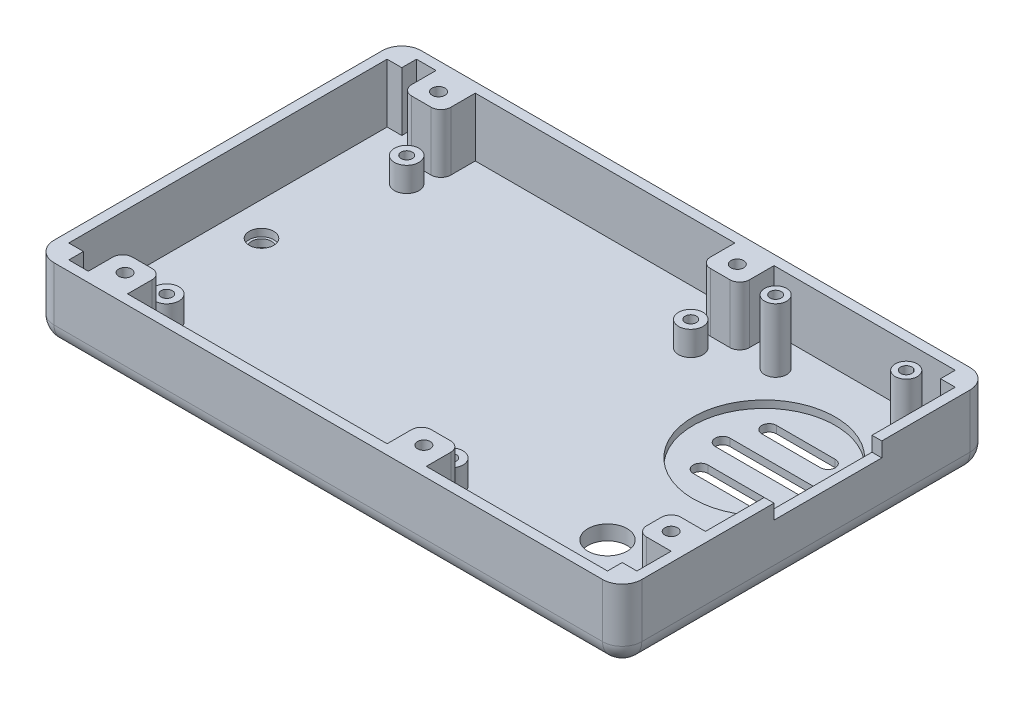
SolidWorks part; units mm, degrees
ref_plane "Front Plane" through (0, 0, 0) normal (0, 0, 1) x (1, 0, 0)
ref_plane "Top Plane" through (0, 0, 0) normal (0, 1, 0) x (1, 0, 0)
ref_plane "Right Plane" through (0, 0, 0) normal (1, 0, 0) x (0, 0, -1)
sketch "Sketch1" plane through (0, 0, 0) normal (0, 1, 0) x (1, 0, 0)
  line L1 (-60, 37.5) -> (60, 37.5)
  line L2 (-60, 37.5) -> (-60, -37.5)
  line L3 (-60, -37.5) -> (60, -37.5)
  line L4 (60, 37.5) -> (60, -37.5)
  line L5 (-60, 37.5) -> (60, -37.5) construction
  line L6 (-60, -37.5) -> (60, 37.5) construction
  point P0 (0, 0)
  dimension "D1" = 120
  dimension "D2" = 75
extrude "Main Structure" add sketch "Sketch1" along normal blind 15
sketch "Sketch2" plane through (0, 15, 0) normal (0, 1, 0) x (1, 0, 0)
  line L1 (-58, -35.5) -> (58, -35.5)
  line L2 (-58, -35.5) -> (-58, 35.5)
  line L3 (-58, 35.5) -> (58, 35.5)
  line L4 (58, -35.5) -> (58, 35.5)
  line L5 (-58, -35.5) -> (58, 35.5) construction
  line L6 (-58, 35.5) -> (58, -35.5) construction
  point P0 (0, 0)
  dimension "D1" = 71
  dimension "D2" = 116
extrude "Inside Cut" cut sketch "Sketch2" against normal blind 12
sketch "Sketch3" plane through (0, 3, 0) normal (0, 1, 0) x (1, 0, 0)
  line L0 (-58, 35.5) -> (-58, -35.5) construction
  line L1 (-58, -35.5) -> (58, -35.5) construction
  line L2 (58, 35.5) -> (-58, 35.5) construction
  circle A0 centre (-46, -24.5) radius 2.5
  circle A1 centre (-46, 24.5) radius 2.5
  circle A2 centre (-46, 24.5) radius 1.15
  circle A3 centre (-46, -24.5) radius 1.15
  circle A4 centre (12, 24.5) radius 2.5
  circle A5 centre (12, -24.5) radius 2.5
  circle A6 centre (12, 24.5) radius 1.15
  circle A7 centre (12, -24.5) radius 1.15
  dimension "D1" = 5
  dimension "D3" = 5
  dimension "D7" = 2.3
  dimension "D8" = 2.3
  dimension "D9" = 5
  dimension "D10" = 5
  dimension "D15" = 2.3
  dimension "D16" = 2.3
  dimension "D2" = 12
  dimension "D4" = 12
  dimension "D5" = 11
  dimension "D6" = 11
  dimension "D11" = 11
  dimension "D12" = 58
  dimension "D13" = 58
  dimension "D14" = 11
extrude "Pi Standoffs" add sketch "Sketch3" along normal blind 5
sketch "Sketch4" plane through (0, 3, 0) normal (0, 1, 0) x (1, 0, 0)
  line L0 (58, -35.5) -> (58, 35.5) construction
  line L1 (-58, -35.5) -> (58, -35.5) construction
  circle A0 centre (48, -30.5) radius 2
  circle A1 centre (48, -17.5) radius 2
  circle A2 centre (48, -17.5) radius 0.9
  circle A3 centre (48, -30.5) radius 0.9
  dimension "D1" = 4
  dimension "D4" = 4
  dimension "D6" = 1.8
  dimension "D7" = 1.8
  dimension "D2" = 10
  dimension "D3" = 5
  dimension "D5" = 13
extrude "Camera Standoffs" add sketch "Sketch4" along normal blind 5
fillet "Body Fillet 1" radius 4 1 edges at (-60, 0, 0)
fillet "Body Fillet 2" radius 4 3 edges at (-60, 9.5, -37.5) (-58.8284, 1.1716, -37.5) (2, 0, -37.5)
fillet "Body Fillet 3" radius 4 3 edges at (-60, 9.5, 37.5) (-58.8284, 1.1716, 37.5) (2, 0, 37.5)
fillet "Body Fillet 4" radius 4 5 edges at (60, 9.5, 37.5) (60, 1.1716, 36.3284) (60, 9.5, -37.5) (60, 1.1716, -36.3284) (60, 0, 0)
sketch "Sketch5" plane through (0, 3, 0) normal (0, 1, 0) x (1, 0, 0)
  line L0 (58, 35.5) -> (-58, 35.5) construction
  line L1 (58, -35.5) -> (58, 35.5) construction
  circle A0 centre (24.33, 29.5) radius 2.25
  circle A1 centre (51, 29.5) radius 2.25
  circle A2 centre (51, 29.5) radius 1.15
  circle A4 centre (24.33, 29.5) radius 1.15
  dimension "D1" = 4.5
  dimension "D3" = 4.5
  dimension "D6" = 2.3
  dimension "D7" = 2.3
  dimension "D2" = 6
  dimension "D4" = 7
  dimension "D5" = 26.67
extrude "Fona Standoffs" add sketch "Sketch5" along normal blind 13
sketch "Sketch6" plane through (0, 3, 0) normal (0, 1, 0) x (1, 0, 0)
  line L1 (-58, -35.5) -> (-55, -35.5)
  line L2 (-58, -35.5) -> (-58, -32.5)
  line L3 (-58, -32.5) -> (-55, -32.5)
  line L4 (-55, -35.5) -> (-55, -32.5)
  line L5 (-58, 35.5) -> (-55, 35.5)
  line L6 (-58, 35.5) -> (-58, 32.5)
  line L7 (-58, 32.5) -> (-55, 32.5)
  line L8 (-55, 35.5) -> (-55, 32.5)
  line L9 (58, -35.5) -> (55, -35.5)
  line L10 (58, -35.5) -> (58, -32.5)
  line L11 (58, -32.5) -> (55, -32.5)
  line L12 (55, -35.5) -> (55, -32.5)
  line L13 (58, 35.5) -> (55, 35.5)
  line L14 (58, 35.5) -> (58, 32.5)
  line L15 (58, 32.5) -> (55, 32.5)
  line L16 (55, 35.5) -> (55, 32.5)
  dimension "D1" = 3
  dimension "D2" = 3
  dimension "D3" = 3
  dimension "D4" = 3
  dimension "D5" = 3
  dimension "D6" = 3
  dimension "D7" = 3
  dimension "D8" = 3
extrude "Corner Support" add sketch "Sketch6" along normal blind 12
sketch "Sketch8" plane through (60, 0, 0) normal (1, 0, 0) x (0, 0, -1)
  line L0 (-33.5, 15) -> (-33.5, 4) construction
  line L1 (-6.5, 15) -> (15.5, 15)
  line L2 (-6.5, 15) -> (-6.5, 12)
  line L3 (-6.5, 12) -> (15.5, 12)
  line L4 (15.5, 15) -> (15.5, 12)
  line L5 (-6.5, 15) -> (15.5, 12) construction
  line L6 (-6.5, 12) -> (15.5, 15) construction
  line L7 (-33.5, 4) -> (33.5, 4) construction
  line L8 (-33.5, 15) -> (33.5, 15) construction
  point P0 (4.5, 13.5)
  dimension "D1" = 27
  dimension "D2" = 8
  dimension "D3" = 0
  dimension "D4" = 22
extrude "Charger Cutout" cut sketch "Sketch8" against normal blind 10
sketch "Sketch9" plane through (0, 3, 0) normal (0, 1, 0) x (1, 0, 0)
  line L1 (-51, -28.5) -> (-43, -28.5)
  line L2 (-51, -28.5) -> (-51, -35.5)
  line L3 (-51, -35.5) -> (-43, -35.5)
  line L4 (-43, -28.5) -> (-43, -35.5)
  line L5 (-51, -28.5) -> (-43, -35.5) construction
  line L6 (-51, -35.5) -> (-43, -28.5) construction
  line L7 (-55, -35.5) -> (55, -35.5) construction
  line L8 (51, -18.5) -> (58, -18.5)
  line L9 (-51, 35.5) -> (-43, 35.5)
  line L10 (-51, 35.5) -> (-51, 28.5)
  line L11 (-51, 28.5) -> (-43, 28.5)
  line L12 (-43, 35.5) -> (-43, 28.5)
  line L13 (-51, 35.5) -> (-43, 28.5) construction
  line L14 (-51, 28.5) -> (-43, 35.5) construction
  line L15 (55, 35.5) -> (-55, 35.5) construction
  line L16 (-58, 32.5) -> (-58, -32.5) construction
  line L17 (58, -32.5) -> (58, 32.5) construction
  line L18 (10, 35.5) -> (18, 35.5)
  line L19 (10, 35.5) -> (10, 28.5)
  line L20 (10, 28.5) -> (18, 28.5)
  line L21 (18, 35.5) -> (18, 28.5)
  line L22 (10, 35.5) -> (18, 28.5) construction
  line L23 (10, 28.5) -> (18, 35.5) construction
  line L24 (51, -18.5) -> (51, -25.5)
  line L25 (10, -28.5) -> (18, -28.5)
  line L26 (10, -28.5) -> (10, -35.5)
  line L27 (10, -35.5) -> (18, -35.5)
  line L28 (18, -28.5) -> (18, -35.5)
  line L29 (10, -28.5) -> (18, -35.5) construction
  line L30 (10, -35.5) -> (18, -28.5) construction
  line L31 (51, -25.5) -> (58, -25.5)
  line L32 (58, -18.5) -> (58, -25.5)
  line L33 (51, -18.5) -> (58, -25.5) construction
  line L34 (51, -25.5) -> (58, -18.5) construction
  point P0 (-47, -32)
  point P9 (54.5, -22)
  point P11 (-47, 32)
  point P16 (14, 32)
  point P29 (14, -32)
  dimension "D5" = 0
  dimension "D10" = 7
  dimension "D16" = 10
  dimension "D2" = 0
  dimension "D3" = 7
  dimension "D4" = 8
  dimension "D6" = 8
  dimension "D7" = 7
  dimension "D8" = 7
  dimension "D9" = 0
  dimension "D11" = 7
  dimension "D12" = 7
  dimension "D13" = 8
  dimension "D14" = 0
  dimension "D15" = 40
  dimension "D17" = 8
  dimension "D18" = 7
  dimension "D19" = 40
  dimension "D20" = 0
extrude "Mounting Structure" add sketch "Sketch9" along normal blind 12
fillet "Mounting Structure Fillet" radius 2 10 edges at (-43, 9, -28.5) (-51, 9, -28.5) (10, 9, -28.5) (18, 9, -28.5) (10, 9, 28.5) (18, 9, 28.5) (-51, 9, 28.5) (-43, 9, 28.5) (51, 9, 18.5) (51, 9, 25.5)
sketch "Sketch10" plane through (0, 15, 0) normal (0, 1, 0) x (1, 0, 0)
  line L0 (-51, 35.5) -> (-51, 30.5) construction
  line L1 (-49, 28.5) -> (-45, 28.5) construction
  line L2 (-51, -30.5) -> (-51, -35.5) construction
  line L3 (-45, -28.5) -> (-49, -28.5) construction
  line L4 (10, -30.5) -> (10, -35.5) construction
  line L5 (16, -28.5) -> (12, -28.5) construction
  line L6 (12, 28.5) -> (16, 28.5) construction
  line L7 (10, 35.5) -> (10, 30.5) construction
  line L8 (51, -20.5) -> (51, -23.5) construction
  line L9 (53, -25.5) -> (58, -25.5) construction
  circle A0 centre (-47, 32) radius 1.3
  circle A1 centre (-47, -32) radius 1.3
  circle A2 centre (14, -32) radius 1.3
  circle A3 centre (14, 32) radius 1.3
  circle A4 centre (54.5, -22) radius 1.3
  point P10 (-47, -28.5)
  dimension "D1" = 2.6
  dimension "D4" = 2.6
  dimension "D7" = 2.6
  dimension "D10" = 2.6
  dimension "D13" = 2.6
  dimension "D2" = 4
  dimension "D3" = 3.5
  dimension "D5" = 4
  dimension "D6" = 3.5
  dimension "D8" = 4
  dimension "D9" = 3.5
  dimension "D11" = 3.5
  dimension "D12" = 4
  dimension "D14" = 3.5
  dimension "D15" = 3.5
extrude "Case Mounting Holes" cut sketch "Sketch10" against normal blind 15
sketch "Sketch13" plane through (0, 0, 0) normal (0, -1, 0) x (1, 0, 0)
  circle A0 centre (-47, 32) radius 2.9
  circle A1 centre (14, 32) radius 2.9
  circle A2 centre (14, -32) radius 2.9
  circle A3 centre (-47, -32) radius 2.9
  circle A4 centre (54.5, 22) radius 2.9
  dimension "D1" = 5.8
  dimension "D2" = 5.8
  dimension "D3" = 5.8
  dimension "D4" = 5.8
  dimension "D5" = 5.8
extrude "Case Screw Head Holes" cut sketch "Sketch13" against normal blind 8.85
sketch "Sketch14" plane through (0, 3, 0) normal (0, 1, 0) x (1, 0, 0)
  line L0 (55, 35.5) -> (18, 35.5) construction
  line L1 (58, -32.5) -> (58, -25.5) construction
  circle A0 centre (39, 12.5) radius 14.5
  dimension "D1" = 29
  dimension "D2" = 23
  dimension "D3" = 19
extrude "Speaker Holder" cut sketch "Sketch14" against normal blind 1.5
sketch "Sketch23" plane through (0, 1.5, 0) normal (0, 1, 0) x (1, 0, 0)
  line L0 (33, 19.5) -> (45, 19.5) construction
  line L1 (33, 21) -> (45, 21)
  line L2 (33, 18) -> (45, 18)
  line L3 (30.5, 12.5) -> (47.5, 12.5) construction
  line L4 (30.5, 14) -> (47.5, 14)
  line L5 (30.5, 11) -> (47.5, 11)
  line L6 (33, 5.5) -> (45, 5.5) construction
  line L7 (33, 7) -> (45, 7)
  line L8 (33, 4) -> (45, 4)
  arc A0 (33, 21) -> (33, 18) centre (33, 19.5) ccw
  arc A1 (45, 18) -> (45, 21) centre (45, 19.5) ccw
  circle A2 centre (39, 12.5) radius 14.5 construction
  arc A3 (30.5, 14) -> (30.5, 11) centre (30.5, 12.5) ccw
  arc A4 (47.5, 11) -> (47.5, 14) centre (47.5, 12.5) ccw
  arc A5 (33, 7) -> (33, 4) centre (33, 5.5) ccw
  arc A6 (45, 4) -> (45, 7) centre (45, 5.5) ccw
  point P2 (39, 19.5)
  point P11 (39, 12.5)
  point P19 (39, 5.5)
  dimension "D3" = 7
  dimension "D1" = 3
  dimension "D2" = 15
  dimension "D4" = 3
  dimension "D5" = 20
  dimension "D6" = 3
  dimension "D7" = 15
  dimension "D8" = 7
extrude "Sound Cutout" cut sketch "Sketch23" against normal blind 1.5
sketch "Sketch25" plane through (0, 3, 0) normal (0, 1, 0) x (1, 0, 0)
  circle A0 centre (-51.1477, 0) radius 2.5
  dimension "D1" = 5
extrude "Microphone holder" cut sketch "Sketch25" against normal blind 1.5
sketch "Sketch26" plane through (0, 1.5, 0) normal (0, 1, 0) x (1, 0, 0)
  circle A0 centre (-51.1477, 0) radius 2
  dimension "D1" = 4
extrude "Microphone Cutout" cut sketch "Sketch26" against normal blind 1.5
sketch "Sketch27" plane through (0, 3, 0) normal (0, 1, 0) x (1, 0, 0)
  line L0 (-58, 32.5) -> (-58, -32.5) construction
  line L1 (55, 35.5) -> (18, 35.5) construction
  circle A0 centre (37.5, -18) radius 4
  dimension "D1" = 8
  dimension "D2" = 95.5
  dimension "D3" = 53.5
extrude "Camera Cutout" cut sketch "Sketch27" against normal blind 10
